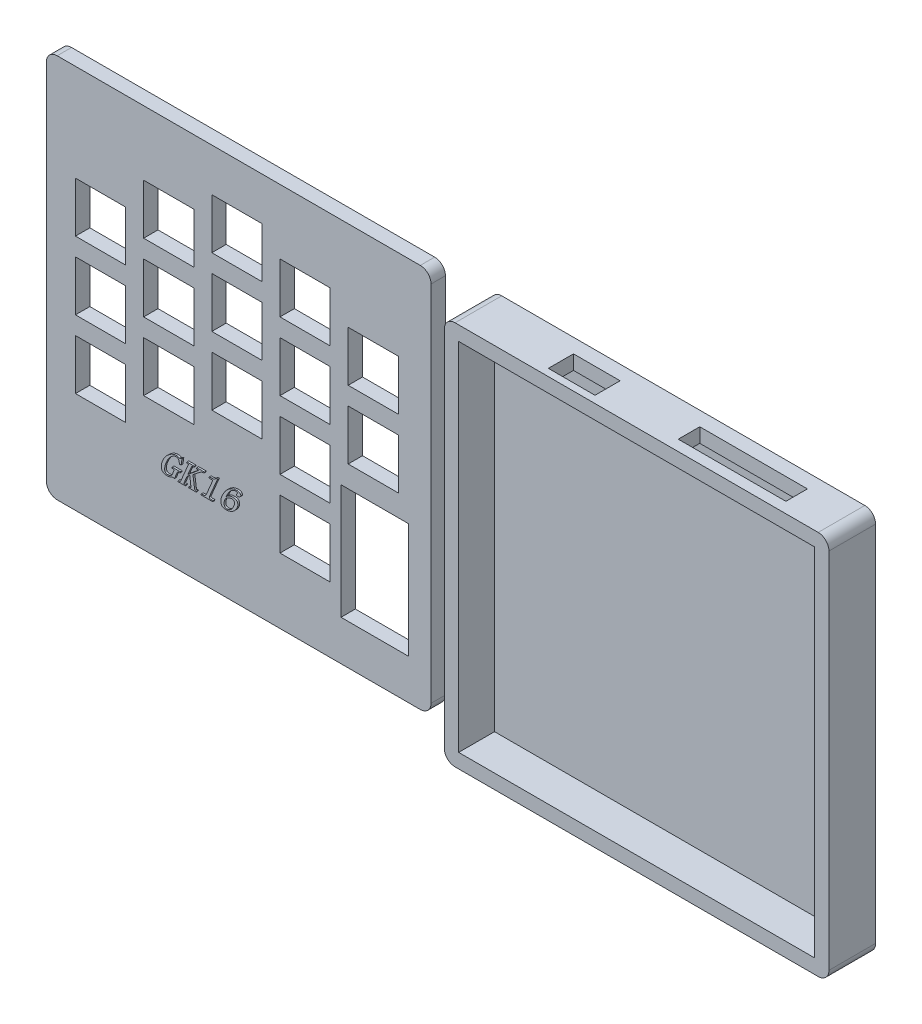
SolidWorks part; units mm, degrees
ref_plane "前视基准面" through (0, 0, 0) normal (0, 0, 1) x (1, 0, 0)
ref_plane "上视基准面" through (0, 0, 0) normal (0, 1, 0) x (1, 0, 0)
ref_plane "右视基准面" through (0, 0, 0) normal (1, 0, 0) x (0, 0, -1)
sketch "Model" plane through (0, 0, 0) normal (0, 0, 1) x (1, 0, 0)
  line L72 (8.101, 61.2137) -> (22.101, 61.2137)
  line L73 (8.101, 42.2137) -> (22.101, 42.2137)
  line L74 (8.101, 42.2137) -> (8.101, 28.2137)
  line L75 (8.101, 28.2137) -> (22.101, 28.2137)
  line L76 (22.101, 42.2137) -> (22.101, 28.2137)
  line L77 (8.101, 61.2137) -> (8.101, 47.2137)
  line L78 (8.101, 47.2137) -> (22.101, 47.2137)
  line L79 (22.101, 61.2137) -> (22.101, 47.2137)
  line L80 (8.101, 80.2137) -> (22.101, 80.2137)
  line L81 (8.101, 80.2137) -> (8.101, 66.2137)
  line L82 (8.101, 66.2137) -> (22.101, 66.2137)
  line L83 (46.101, 43.2137) -> (60.101, 43.2137)
  line L84 (27.101, 37.2137) -> (41.101, 37.2137)
  line L85 (27.101, 37.2137) -> (27.101, 51.2137)
  line L86 (27.101, 51.2137) -> (41.101, 51.2137)
  line L87 (22.101, 80.2137) -> (22.101, 66.2137)
  line L88 (41.101, 37.2137) -> (41.101, 51.2137)
  line L89 (46.101, 43.2137) -> (46.101, 57.2137)
  line L90 (46.101, 57.2137) -> (60.101, 57.2137)
  line L91 (60.101, 43.2137) -> (60.101, 57.2137)
  line L92 (65.101, 18.2137) -> (79.101, 18.2137)
  line L93 (65.101, 18.2137) -> (65.101, 32.2137)
  line L94 (65.101, 32.2137) -> (79.101, 32.2137)
  line L95 (79.101, 18.2137) -> (79.101, 32.2137)
  line L96 (84.101, 49.2137) -> (98.101, 49.2137)
  line L97 (84.101, 49.2137) -> (84.101, 63.2137)
  line L98 (84.101, 63.2137) -> (98.101, 63.2137)
  line L99 (98.101, 49.2137) -> (98.101, 63.2137)
  line L100 (27.101, 56.2137) -> (41.101, 56.2137)
  line L101 (27.101, 56.2137) -> (27.101, 70.2137)
  line L102 (27.101, 70.2137) -> (41.101, 70.2137)
  line L103 (41.101, 56.2137) -> (41.101, 70.2137)
  line L104 (27.101, 75.2137) -> (41.101, 75.2137)
  line L105 (27.101, 75.2137) -> (27.101, 89.2137)
  line L106 (27.101, 89.2137) -> (41.101, 89.2137)
  line L107 (41.101, 75.2137) -> (41.101, 89.2137)
  line L108 (46.101, 62.2137) -> (60.101, 62.2137)
  line L109 (46.101, 62.2137) -> (46.101, 76.2137)
  line L110 (46.101, 76.2137) -> (60.101, 76.2137)
  line L111 (60.101, 62.2137) -> (60.101, 76.2137)
  line L112 (46.101, 81.2137) -> (60.101, 81.2137)
  line L113 (46.101, 81.2137) -> (46.101, 95.2137)
  line L114 (46.101, 95.2137) -> (60.101, 95.2137)
  line L115 (60.101, 81.2137) -> (60.101, 95.2137)
  line L116 (65.101, 37.2137) -> (79.101, 37.2137)
  line L117 (65.101, 37.2137) -> (65.101, 51.2137)
  line L118 (65.101, 51.2137) -> (79.101, 51.2137)
  line L119 (79.101, 37.2137) -> (79.101, 51.2137)
  line L120 (65.101, 56.2137) -> (79.101, 56.2137)
  line L121 (65.101, 56.2137) -> (65.101, 70.2137)
  line L122 (65.101, 70.2137) -> (79.101, 70.2137)
  line L123 (79.101, 56.2137) -> (79.101, 70.2137)
  line L124 (65.101, 75.2137) -> (79.101, 75.2137)
  line L125 (65.101, 75.2137) -> (65.101, 89.2137)
  line L126 (65.101, 89.2137) -> (79.101, 89.2137)
  line L127 (79.101, 75.2137) -> (79.101, 89.2137)
  line L128 (84.101, 68.2137) -> (98.101, 68.2137)
  line L129 (84.101, 68.2137) -> (84.101, 82.2137)
  line L130 (84.101, 82.2137) -> (98.101, 82.2137)
  line L131 (98.101, 68.2137) -> (98.101, 82.2137)
  line L133 (100.9211, 43.2137) -> (82.101, 43.2137)
  line L134 (100.9211, 43.2137) -> (100.9211, 11.2137)
  line L135 (100.9211, 11.2137) -> (82.101, 11.2137)
  line L136 (82.101, 43.2137) -> (82.101, 11.2137)
  line L155 (0, 0) -> (107.2, 0)
  line L156 (0, 0) -> (0, 107.2)
  line L157 (0, 107.2) -> (107.2, 107.2)
  line L158 (107.2, 0) -> (107.2, 107.2)
  point P78 (8.101, 42.2137)
  point P79 (22.101, 28.2137)
  point P84 (27.101, 37.2137)
  point P88 (8.101, 61.2137)
  point P89 (22.101, 47.2137)
  point P94 (8.101, 80.2137)
  point P95 (22.101, 66.2137)
  point P97 (46.101, 43.2137)
  point P98 (65.101, 18.2137)
  point P99 (82.101, 11.2137)
  point P100 (100.9211, 43.2137)
  point P101 (84.101, 49.2137)
  point P107 (46.101, 43.2137)
  point P113 (65.101, 18.2137)
  point P117 (27.101, 56.2137)
  point P118 (84.101, 49.2137)
  point P121 (84.101, 49.2137)
  point P126 (46.101, 62.2137)
  point P129 (27.101, 75.2137)
  point P134 (46.101, 62.2137)
  point P137 (46.101, 81.2137)
  point P140 (46.101, 81.2137)
  point P143 (65.101, 37.2137)
  point P146 (65.101, 37.2137)
  point P149 (65.101, 56.2137)
  point P152 (65.101, 56.2137)
  point P156 (65.101, 75.2137)
  point P159 (65.101, 75.2137)
  point P163 (84.101, 68.2137)
  point P164 (84.101, 68.2137)
  point P167 (84.101, 68.2137)
  point P172 (0, 0)
  dimension "D1" = 107.2
  dimension "D2" = 14
  dimension "D3" = 8.101
  dimension "D4" = 28.2137
  dimension "D5" = 5
  dimension "D6" = 5
  dimension "D7" = 9
  dimension "D8" = 14
  dimension "D9" = 14
  dimension "D10" = 14
  dimension "D11" = 14
  dimension "D12" = 18.2137
  dimension "D13" = 6
  dimension "D14" = 5
  dimension "D15" = 42.099
  dimension "D16" = 14
  dimension "D17" = 23.099
  dimension "D18" = 17
  dimension "D19" = 14
  dimension "D20" = 14
  dimension "D21" = 14
  dimension "D22" = 3
  dimension "D25" = 11.2137
  dimension "D26" = 6.2789
  dimension "D27" = 32
  dimension "D28" = 18.82
  dimension "D23" = 3
  dimension "D24" = 2
extrude "凸台-拉伸1" add sketch "Model" along normal blind 4
sketch "草图3" plane through (0, 0, 0) normal (0, 0, 1) x (1, 0, 0)
  line L1 (107.2, 0) -> (107.2, 107.2) construction
  line L2 (119.8958, 0) -> (227.0958, 0)
  line L3 (119.8958, 0) -> (119.8958, 107.2)
  line L4 (119.8958, 107.2) -> (227.0958, 107.2)
  line L8 (227.0958, 0) -> (227.0958, 107.2)
  line L9 (0, 0) -> (107.2, 0) construction
extrude "凸台-拉伸2" add sketch "草图3" along normal blind 13 separate body contours L3 L4 L8 L2
sketch "草图6" plane through (0, 0, 13) normal (0, 0, 1) x (1, 0, 0)
  line L14 (123.8958, 4) -> (223.0958, 4)
  line L15 (223.0958, 4) -> (223.0958, 103.2)
  line L16 (223.0958, 103.2) -> (123.8958, 103.2)
  line L17 (123.8958, 103.2) -> (123.8958, 4)
  line L18 (123.8958, 4) -> (223.0958, 4)
  line L19 (223.0958, 4) -> (223.0958, 103.2)
  line L20 (223.0958, 103.2) -> (123.8958, 103.2)
  line L21 (123.8958, 103.2) -> (123.8958, 4)
  dimension "D1" = 4
extrude "切除-拉伸1" cut sketch "草图6" against normal blind 10
sketch "草图9" plane through (0, 107.2, 0) normal (0, 1, 0) x (1, 0, 0)
  line L0 (227.0958, -13) -> (227.0958, 0) construction
  line L1 (182.0958, -4) -> (212.0958, -4)
  line L2 (182.0958, -4) -> (182.0958, -10)
  line L3 (182.0958, -10) -> (212.0958, -10)
  line L4 (212.0958, -4) -> (212.0958, -10)
  line L5 (146.8958, -4) -> (159.8958, -4)
  line L6 (146.8958, -4) -> (146.8958, -11)
  line L7 (146.8958, -11) -> (159.8958, -11)
  line L8 (159.8958, -4) -> (159.8958, -11)
  line L9 (119.8958, -13) -> (227.0958, -13) construction
  line L10 (119.8958, -13) -> (119.8958, 0) construction
  line L11 (119.8958, 0) -> (227.0958, 0) construction
  dimension "D1" = 15
  dimension "D2" = 3
  dimension "D3" = 6
  dimension "D4" = 30
  dimension "D5" = 27
  dimension "D6" = 4
  dimension "D7" = 13
  dimension "D8" = 7
extrude "切除-拉伸2" cut sketch "草图9" against normal blind 4
fillet "圆角1" radius 3 4 edges at (107.2, 0, 2) (0, 0, 2) (107.2, 107.2, 2) (0, 107.2, 2)
fillet "圆角2" radius 3 4 edges at (119.8958, 0, 6.5) (227.0958, 0, 6.5) (119.8958, 107.2, 6.5) (227.0958, 107.2, 6.5)
sketch "草图10" plane through (0, 0, 4) normal (0, 0, 1) x (1, 0, 0)
  text T0 "GK16" font "@隶书" height 6
extrude "凸台-拉伸3" add sketch "草图10" along normal blind 0.5
ref_plane "基准面4" through (-200.8176, 107.2, 3) normal (-1, 0, 0) x (0, 0, 1)
